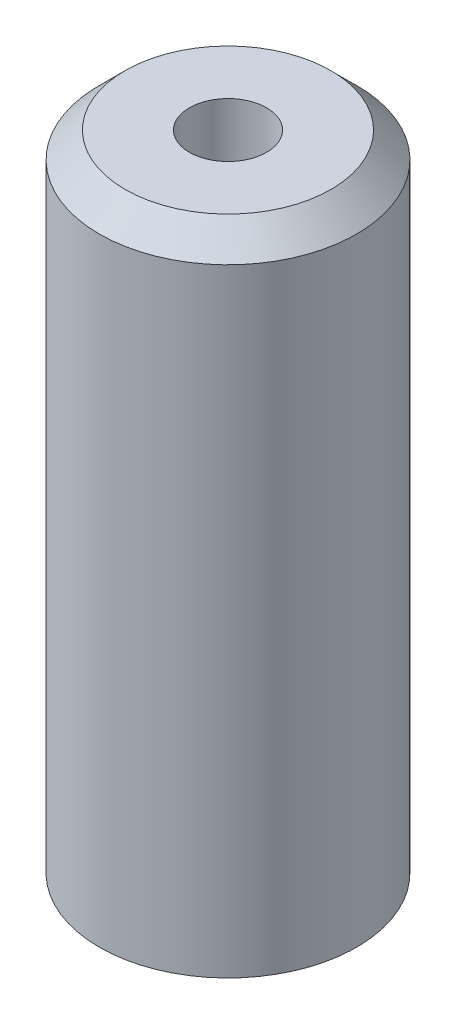
SolidWorks part; units mm, degrees
ref_plane "Front Plane" through (0, 0, 0) normal (0, 0, 1) x (1, 0, 0)
ref_plane "Top Plane" through (0, 0, 0) normal (0, 1, 0) x (1, 0, 0)
ref_plane "Right Plane" through (0, 0, 0) normal (1, 0, 0) x (0, 0, -1)
sketch "Sketch2" plane through (0, 0, 0) normal (0, 0, 1) x (1, 0, 0)
  line L0 (0, 0) -> (4, 0)
  line L1 (4, 0) -> (5, -1)
  line L2 (5, -1) -> (5, -25)
  line L3 (5, -25) -> (0, -25)
  line L4 (0, -25) -> (0, 0)
  line L5 (4, 0) -> (22.7031, 0) construction
  line L6 (0, 3.5845) -> (0, -33.2223) construction
  dimension "D1" = 45
  dimension "D2" = 5
  dimension "D3" = 25
  dimension "D4" = 4
revolve "Revolve1" add sketch "Sketch2" angle 360 about L6
cosmetic thread "Cosmetic Thread8" parameters "D1"=10, "D2"=8.344
hole_wizard "Ø6.0 (6) Diameter Hole1" positions "Sketch5" profile "Sketch4" hole size "Ø6.0" standard "ISO"
sketch "Sketch5" plane through (0, -25, 0) normal (0, -1, 0) x (-1, 0, 0)
  point P0 (0, 0)
sketch "Sketch4" plane through (0, -25, 0) normal (1, 0, 0) x (0, 0, -1)
  line L0 (0, 0) -> (0, 21.8026)
  line L1 (0, 21.8026) -> (3, 20)
  line L2 (3, 20) -> (3, 0)
  line L5 (3, 0) -> (0, 0)
  line L10 (0, 21.8026) -> (-3, 20) construction
  line L11 (0, -6.35) -> (0, 107.95) construction
  dimension "Hole Dia." = 6
  dimension "Hole Depth" = 20
  dimension "Drill Angle" = 118
cosmetic thread "Cosmetic Thread6" parameters "D1"=10, "D2"=8
sketch "Sketch6" plane through (0, 0, 0) normal (0, 1, 0) x (1, 0, 0)
  circle A0 centre (0, 0) radius 1.5
  dimension "D1" = 3
extrude "Cut-Extrude1" cut sketch "Sketch6" against normal through all
sketch "Sketch7" plane through (0, -25, 0) normal (0, -1, 0) x (-1, 0, 0)
  circle A0 centre (0, 0) radius 3
  dimension "D1" = 6
